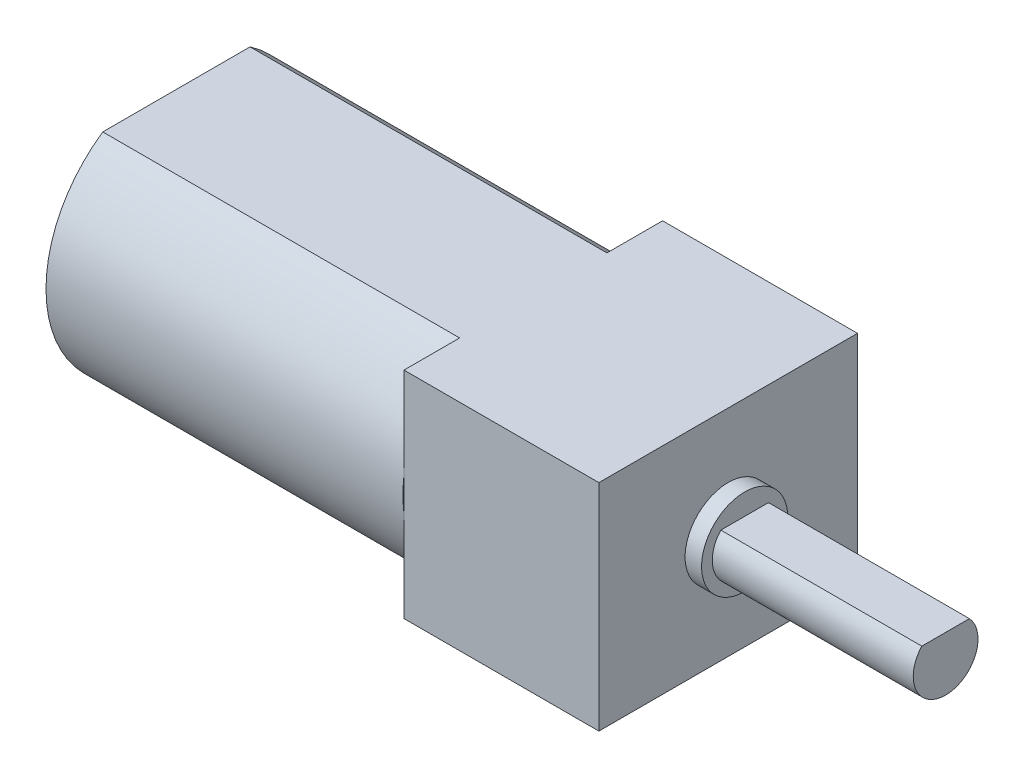
SolidWorks part; units mm, degrees
ref_plane "Front Plane" through (0, 0, 0) normal (0, 0, 1) x (1, 0, 0)
ref_plane "Top Plane" through (0, 0, 0) normal (0, 1, 0) x (1, 0, 0)
ref_plane "Right Plane" through (0, 0, 0) normal (1, 0, 0) x (0, 0, -1)
sketch "Sketch1" plane through (0, 0, 0) normal (1, 0, 0) x (0, 0, -1)
  line L1 (-5.9817, 4.9784) -> (5.9817, 4.9784)
  line L2 (-5.9817, 4.9784) -> (-5.9817, -4.9784)
  line L3 (-5.9817, -4.9784) -> (5.9817, -4.9784)
  line L4 (5.9817, 4.9784) -> (5.9817, -4.9784)
  line L5 (-5.9817, 4.9784) -> (5.9817, -4.9784) construction
  line L6 (-5.9817, -4.9784) -> (5.9817, 4.9784) construction
  point P0 (0, 0)
  dimension "D1" = 11.9634
  dimension "D2" = 9.9568
extrude "Boss-Extrude1" add sketch "Sketch1" against normal blind 9.017
sketch "Sketch2" plane through (0, 0, 0) normal (1, 0, 0) x (0, 0, -1)
  line L0 (-1.1016, 1.016) -> (1.1016, 1.016)
  line L1 (2.8107, -1.4986) -> (-2.4122, -1.4986) construction
  arc A0 (-1.1016, 1.016) -> (1.1016, 1.016) centre (0, 0) ccw
  dimension "D1" = 2.9972
  dimension "D2" = 2.5146
extrude "Boss-Extrude2" add sketch "Sketch2" along normal blind 10.0584
sketch "Sketch3" plane through (0, 0, 0) normal (1, 0, 0) x (0, 0, -1)
  circle A0 centre (0, 0) radius 1.9939
  dimension "D1" = 3.9878
extrude "Boss-Extrude3" add sketch "Sketch3" along normal blind 0.762
sketch "Sketch4" plane through (-9.017, 0, 0) normal (-1, 0, 0) x (0, 0, 1)
  line L0 (-3.4068, 4.9784) -> (3.4068, 4.9784)
  line L1 (-5.9817, 4.9784) -> (5.9817, 4.9784) construction
  line L2 (-3.4068, -4.9784) -> (3.4068, -4.9784)
  line L3 (5.9817, -4.9784) -> (-5.9817, -4.9784) construction
  arc A0 (-3.4068, 4.9784) -> (-3.4068, -4.9784) centre (0, 0) ccw
  arc A1 (3.4068, -4.9784) -> (3.4068, 4.9784) centre (0, 0) ccw
  dimension "D1" = 12.065
extrude "Boss-Extrude4" add sketch "Sketch4" along normal blind 16.51
